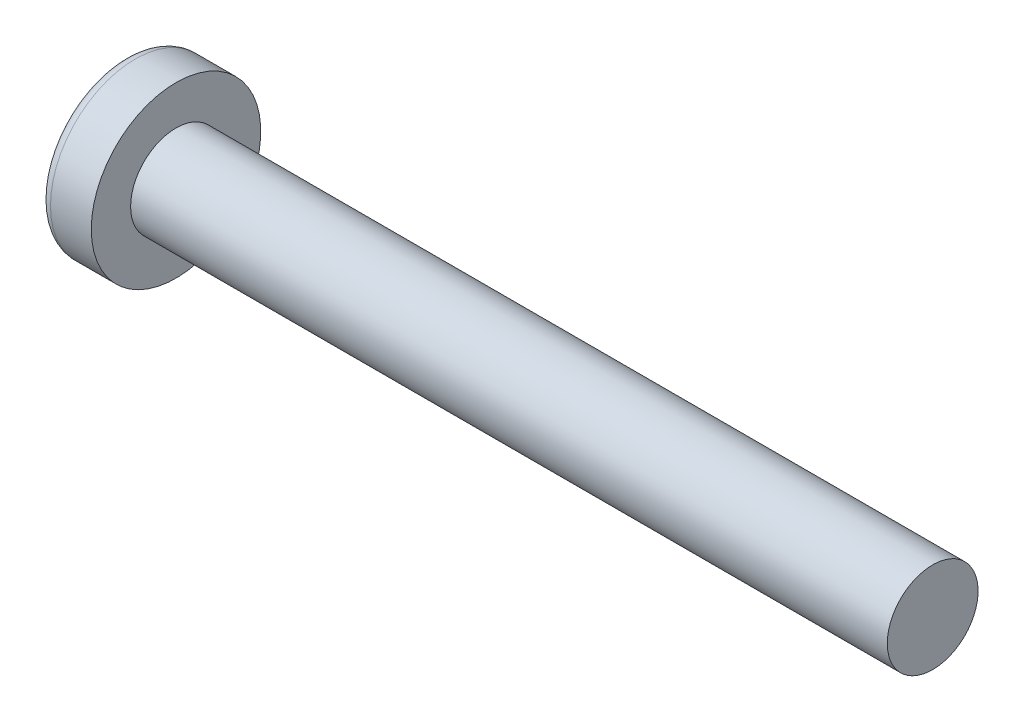
SolidWorks part; units mm, degrees
ref_plane "Plane1" through (0, 0, 0) normal (0, 0, 1) x (1, 0, 0)
ref_plane "Plane2" through (0, 0, 0) normal (0, 1, 0) x (1, 0, 0)
ref_plane "Plane3" through (0, 0, 0) normal (1, 0, 0) x (0, 0, -1)
sketch "BodySke" plane through (0, 0, 0) normal (0, 0, 1) x (1, 0, 0)
  line L0 (2.4, 1.5) -> (2.4, 2.8)
  line L1 (2.9, 6.35) -> (2.9, -3.175) construction
  line L2 (-25.4, 0) -> (127, 0) construction
  line L3 (27.4, 0) -> (0, 0)
  line L4 (2.4, 1.5) -> (27.4, 1.5)
  line L5 (27.4, 1.5) -> (27.4, 0)
  line L6 (1.0534, 2.8) -> (2.4, 2.8)
  line L7 (2.4, -1.5) -> (27.4, -1.5) construction
  line L8 (2.4, 6.35) -> (2.4, -3.175) construction
  arc A0 (0.7472, 2.6293) -> (0, 0) centre (5, 0) ccw
  arc A2 (0.7472, 2.6293) -> (1.0534, 2.8) centre (1.0534, 2.44) cw
  dimension "Head_fillet_rad" = 0.36
  dimension "Head_crown_rad" = 5
  dimension "Head_ht" = 2.4
  dimension "Diameter" = 3
  dimension "Length" = 25
  dimension "Head_dia" = 5.6
  dimension "Advance" = 0.5
  dimension "Thread_nom" = 25
revolve "Base-Revolve" add sketch "BodySke" angle 360 about L2
cosmetic thread "ThreadCosmetic" parameters "Thread_length"=24.5, "Thread_minor"=2.439
sketch "Sketch3" plane through (0, 0, 0) normal (1, 0, 0) x (0, 0, -1)
  line L0 (0.37, -1.45) -> (-0.37, -1.45)
  line L1 (0.37, -1.45) -> (0.37, 1.45)
  line L2 (-0.37, 1.45) -> (0.37, 1.45)
  line L3 (-0.37, 1.45) -> (-0.37, -1.45)
  dimension "D1" = 1.45
  dimension "Cross_dia" = 2.9
  dimension "D2" = 0.37
  dimension "Cross_width" = 0.74
ref_plane "Plane4" through (1.76, 0, 0) normal (1, 0, 0) x (0, 0, -1)
sketch "Sketch4" plane through (1.76, 0, 0) normal (1, 0, 0) x (0, 0, -1)
  line L0 (0.185, -0.185) -> (-0.185, -0.185)
  line L1 (0.185, -0.185) -> (0.185, 0.185)
  line L2 (-0.185, 0.185) -> (0.185, 0.185)
  line L3 (-0.185, 0.185) -> (-0.185, -0.185)
  dimension "D1" = 0.37
  dimension "D2" = 0.37
  dimension "D3" = 0.185
  dimension "D4" = 0.185
loft "Cut-Loft1" cut profiles "Sketch3", "Sketch4"
pattern_circular "CirPattern1" count 2 every 90 about axis through (0, 0, 0) along (1, 0, 0) of "Cut-Loft1"
sketch "ThdSchSke" plane through (0, 0, 0) normal (0, 0, 1) x (1, 0, 0)
  line L0 (2.9, -1.2195) -> (2.7036, -1.5)
  line L1 (2.9, -1.2195) -> (3.0964, -1.5)
  line L2 (3.0964, -1.5) -> (3.0964, -1.875)
  line L3 (-3.175, 0) -> (5.1513, 0) construction
  line L5 (3.0964, -1.875) -> (2.7036, -1.875)
  line L6 (2.7036, -1.875) -> (2.7036, -1.5)
  dimension "Thread_minor" = 2.439
  dimension "Diameter" = 3
  dimension "Start" = 2.9
  dimension "SideAngle" = 55
  dimension "VeeAngle" = 70
  dimension "Overcut" = 3.75
revolve "ThreadSchematic" [suppressed] cut sketch "ThdSchSke" angle 360 about L3
pattern_linear "ThdSchPat" [suppressed]
equation "\"D1@Sketch3\" = \"Cross_dia@Sketch3\" / 2"
equation "\"D2@Sketch3\" = \"Cross_width@Sketch3\" / 2"
equation "\"D1@Sketch4\" = \"Cross_width@Sketch3\" *.5"
equation "\"D2@Sketch4\" = \"D1@Sketch4\""
equation "\"D3@Sketch4\" = \"D1@Sketch4\" / 2"
equation "\"D4@Sketch4\" = \"D2@Sketch4\" / 2"
equation "\"Thread_length@ThreadCosmetic\" = ((sgn( (\"Length@BodySke\" - \"Advance@BodySke\" ) - \"Thread_nom@BodySke\" )-1)*( (\"Length@BodySke\" - \"Advance@BodySke\" ) - \"Thread_nom@BodySke\" ))/-2+ \"Thread_nom@BodySke\""
equation "\"Thread_minor@ThdSchSke\" = \"Thread_minor@ThreadCosmetic\""
equation "\"Diameter@ThdSchSke\" = \"Diameter@BodySke\""
equation "\"Overcut@ThdSchSke\" = \"Diameter@BodySke\" * 1.25"
equation "\"Start@ThdSchSke\" = \"Head_ht@BodySke\" + \"Length@BodySke\" - \"Thread_length@ThreadCosmetic\"  '---Non-countersunk---"
equation "\"Num_threads@ThdSchPat\" = int( \"Thread_length@ThreadCosmetic\" / \"Advance@BodySke\" + 0.999 )  + 1"
equation "\"Advance@ThdSchPat\" = \"Thread_length@ThreadCosmetic\" /  (\"Num_threads@ThdSchPat\" - 1) 'relax it"
